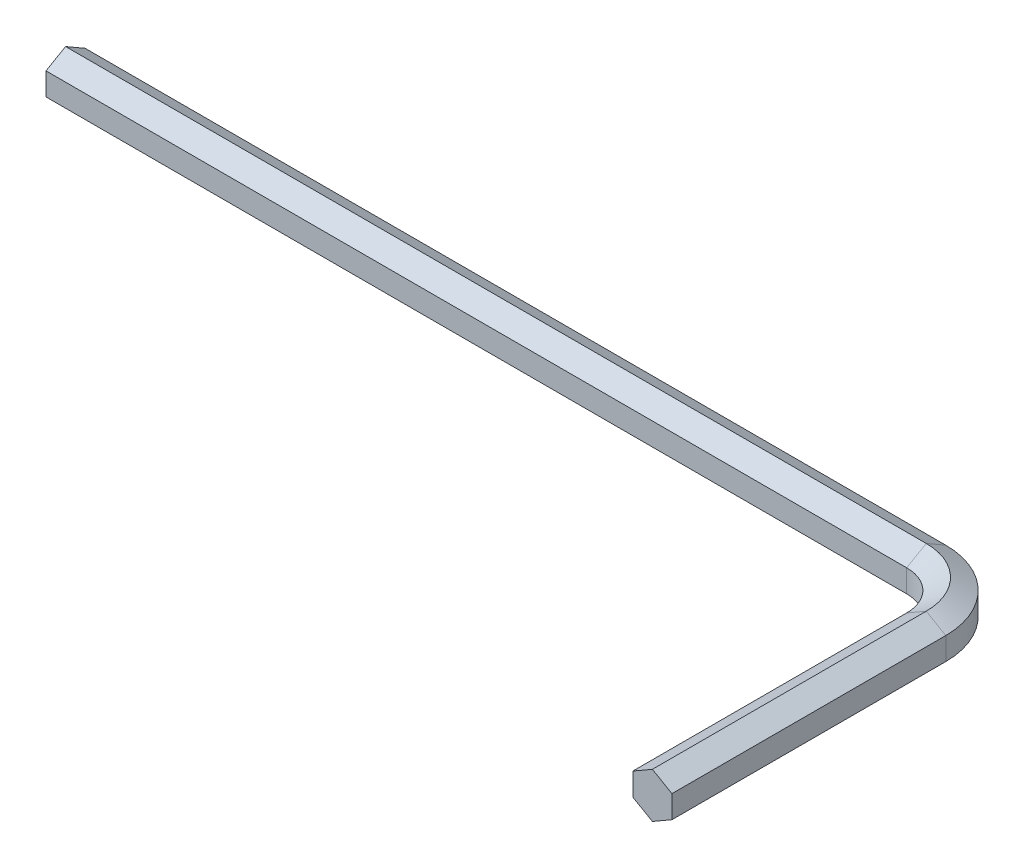
SolidWorks part; units mm, degrees
ref_plane "Front Plane" through (0, 0, 0) normal (0, 0, 1) x (1, 0, 0)
ref_plane "Top Plane" through (0, 0, 0) normal (0, 1, 0) x (1, 0, 0)
ref_plane "Right Plane" through (0, 0, 0) normal (1, 0, 0) x (0, 0, -1)
sketch "Sketch1" plane through (0, 0, 0) normal (0, 0, 1) x (1, 0, 0)
  line L1 (0, 1.1547) -> (-1, 0.5774)
  line L2 (-1, 0.5774) -> (-1, -0.5774)
  line L3 (-1, -0.5774) -> (0, -1.1547)
  line L4 (0, -1.1547) -> (1, -0.5774)
  line L5 (1, -0.5774) -> (1, 0.5774)
  line L6 (1, 0.5774) -> (0, 1.1547)
  circle A0 centre (0, 0) radius 1 construction
  dimension "D1" = 2
sketch "Sketch2" plane through (0, 0, 0) normal (0, 1, 0) x (1, 0, 0)
  line L0 (0, 0) -> (0, 14)
  line L1 (-1, 0) -> (1, 0) construction
  line L2 (-3, 17) -> (-47, 17)
  arc A0 (0, 14) -> (-3, 17) centre (-3, 14) ccw
  point P7 (0, 17)
  dimension "D3" = 3
  dimension "D1" = 17
  dimension "D2" = 47
sweep "Sweep1" add profiles "Sketch1" path "Sketch2"
